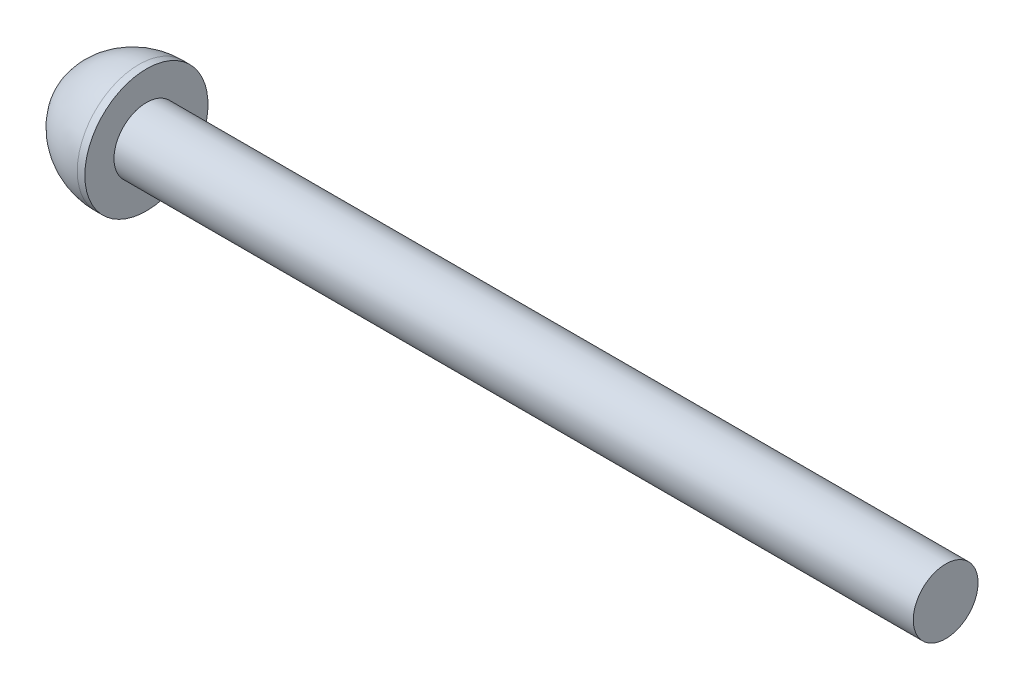
SolidWorks part; units mm, degrees
ref_plane "Front Plane" through (0, 0, 0) normal (0, 0, 1) x (1, 0, 0)
ref_plane "Top Plane" through (0, 0, 0) normal (0, 1, 0) x (1, 0, 0)
ref_plane "Right Plane" through (0, 0, 0) normal (1, 0, 0) x (0, 0, -1)
sketch "Sketch1" plane through (0, 0, 0) normal (0, 0, 1) x (1, 0, 0)
  line L0 (0, 0) -> (49.4446, 0) construction
  line L1 (0, 0) -> (0, 1.43)
  line L2 (2.8149, 2.85) -> (3.1649, 2.85)
  line L3 (3.1649, 2.85) -> (3.1649, 1.5)
  line L4 (3.1649, 1.5) -> (40.1649, 1.5)
  line L5 (40.1649, 1.5) -> (40.1649, 0)
  line L6 (0, 0) -> (40.1649, 0)
  arc A0 (0, 1.43) -> (2.8149, 2.85) centre (2.8149, -0.65) cw
  dimension "D2" = 3.5
  dimension "D1" = 37
  dimension "D3" = 2.85
  dimension "D4" = 1.43
  dimension "D5" = 0.35
  dimension "D6" = 1.5
revolve "Revolve1" add sketch "Sketch1" angle 360 about L0
sketch "Sketch2" plane through (0, 0, 0) normal (-1, 0, 0) x (0, 0, 1)
  line L1 (1, 0) -> (0.5, 0.866)
  line L2 (0.5, 0.866) -> (-0.5, 0.866)
  line L3 (-0.5, 0.866) -> (-1, 0)
  line L4 (-1, 0) -> (-0.5, -0.866)
  line L5 (-0.5, -0.866) -> (0.5, -0.866)
  line L6 (0.5, -0.866) -> (1, 0)
  circle A0 centre (0, 0) radius 0.866 construction
  dimension "D1" = 2
extrude "Cut-Extrude1" cut sketch "Sketch2" against normal blind 1
scale "Scale1" scale about centroid uniform scaling yes scale factor 1.7
